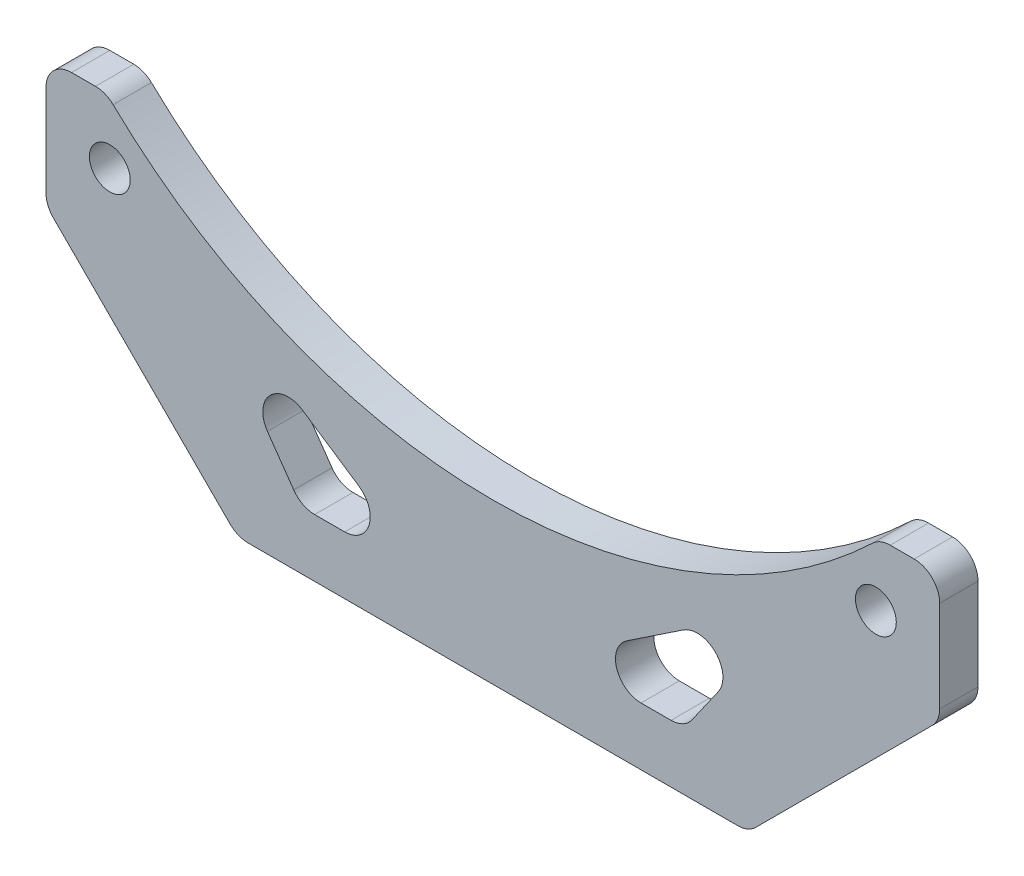
SolidWorks part; units mm, degrees
material "A-玻璃纤维"
ref_plane "前视基准面" through (0, 0, 0) normal (0, 0, 1) x (1, 0, 0)
ref_plane "上视基准面" through (0, 0, 0) normal (0, 1, 0) x (1, 0, 0)
ref_plane "右视基准面" through (0, 0, 0) normal (1, 0, 0) x (0, 0, -1)
sketch "草图1" plane through (0, 0, 0) normal (0, 0, 1) x (1, 0, 0)
  line L0 (0, 0) -> (60, 0) construction
  line L1 (45.025, 5) -> (65, 5)
  line L2 (-5, 5) -> (14.975, 5)
  line L3 (-5, 5) -> (-5, -5)
  line L4 (-5, -5) -> (65, -5) construction
  line L5 (65, 5) -> (65, -5)
  line L6 (-5, 5) -> (65, -5) construction
  line L7 (-5, -5) -> (65, 5) construction
  line L8 (-5, -5) -> (10, -20)
  line L9 (10, -20) -> (50, -20)
  line L10 (50, -20) -> (65, -5)
  line L11 (30, 0) -> (30, 35.5) construction
  circle A0 centre (60, 0) radius 1.6
  circle A1 centre (0, 0) radius 1.6
  arc A2 (14.975, 5) -> (45.025, 5) centre (30, 35.5) ccw
  point P5 (30, 0)
  dimension "D1" = 3.2
  dimension "D6" = 68
  dimension "D2" = 60
  dimension "D3" = 70
  dimension "D4" = 10
  dimension "D5" = 35.5
  dimension "D7" = 15
  dimension "D8" = 40
extrude "凸台-拉伸1" add sketch "草图1" along normal blind 3
sketch "草图3" plane through (0, 0, 0) normal (0, 0, -1) x (-1, 0, 0)
  line L0 (-30, -20) -> (-30, 14.794) construction
  line L1 (-10, -20) -> (-50, -20) construction
  line L2 (-60, 0) -> (0, 0) construction
  line L3 (0, 0) -> (-30, -20) construction
  line L4 (-30, -20) -> (-60, 0) construction
  line L5 (-30, -12.7889) -> (-40.1833, -6) construction
  line L6 (-40.1833, -6) -> (-19.8167, -6) construction
  line L7 (-19.8167, -6) -> (-30, -12.7889) construction
  line L8 (-48, -4) -> (-33, -4) construction
  line L9 (-33, -4) -> (-52.3507, 1.185) construction
  line L10 (-52.3507, 1.185) -> (-48, -4) construction
  line L11 (-25, -15.4648) -> (-15, -15.4648)
  line L12 (-15, -15.4648) -> (-6.2451, -2.9616)
  line L13 (-6.2451, -2.9616) -> (-25, -15.4648)
  line L14 (-27, -4) -> (-7.6493, 1.185) construction
  line L15 (-7.6493, 1.185) -> (-12, -4) construction
  line L16 (-12, -4) -> (-27, -4) construction
  line L17 (-53.7549, -2.9616) -> (-35, -15.4648)
  line L18 (-45, -15.4648) -> (-53.7549, -2.9616)
  line L19 (-35, -15.4648) -> (-45, -15.4648)
  dimension "D2" = 5
  dimension "D3" = 10
  dimension "D4" = 5
  dimension "D5" = 125
  dimension "D6" = 3
  dimension "D7" = 15
  dimension "D8" = 130
  dimension "D9" = 4
  dimension "D10" = 35
  dimension "D1" = 6
extrude "切除-拉伸1" cut sketch "草图3" against normal through all
sketch "草图4" plane through (0, 0, 3) normal (0, 0, 1) x (1, 0, 0)
  circle A0 centre (30, 35.5) radius 43
  dimension "D1" = 86
extrude "切除-拉伸2" cut sketch "草图4" against normal blind 10
fillet "圆角1" radius 2 14 edges at (53.7549, -2.9616, 1.5) (35, -15.4648, 1.5) (45, -15.4648, 1.5) (6.2451, -2.9616, 1.5) (15, -15.4648, 1.5) (25, -15.4648, 1.5) (60.3109, 5, 1.5) (65, 5, 1.5) (65, -5, 1.5) (50, -20, 1.5) (10, -20, 1.5) (-5, -5, 1.5) (-0.3109, 5, 1.5) (-5, 5, 1.5)
